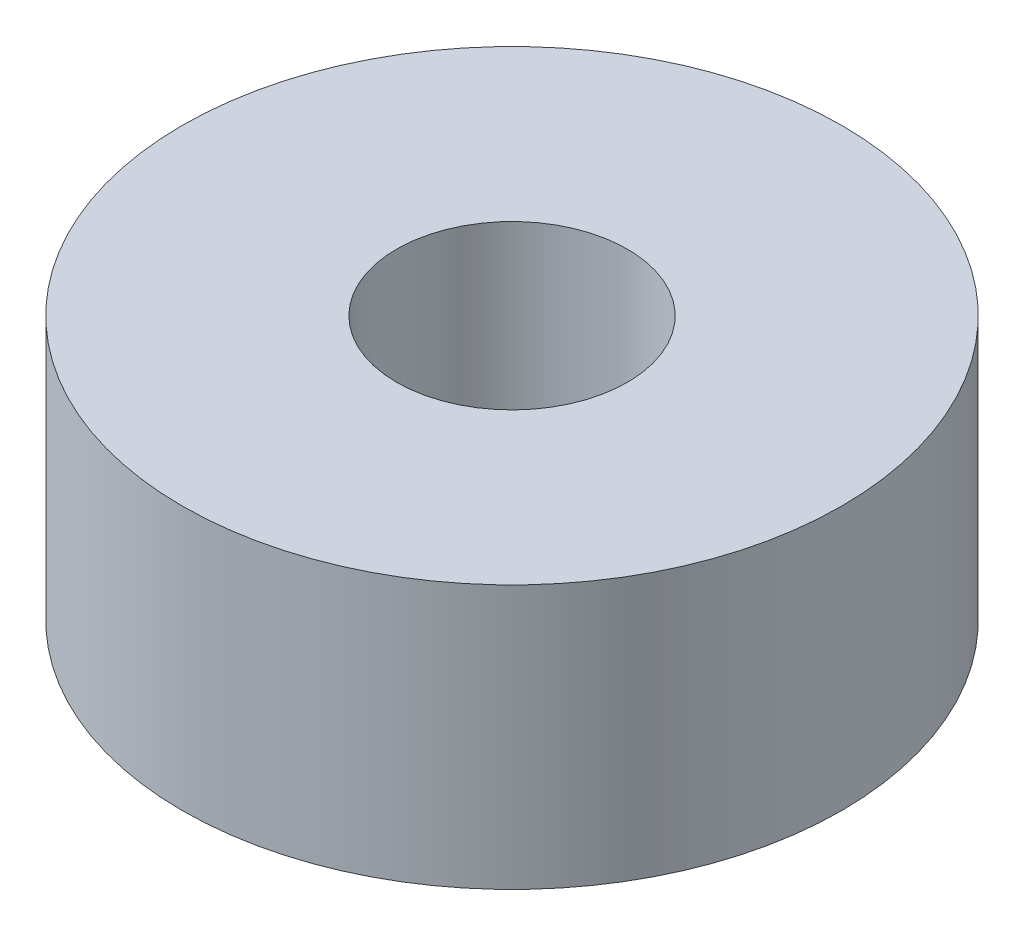
SolidWorks part; units mm, degrees
ref_plane "Front Plane" through (0, 0, 0) normal (0, 0, 1) x (1, 0, 0)
ref_plane "Top Plane" through (0, 0, 0) normal (0, 1, 0) x (1, 0, 0)
ref_plane "Right Plane" through (0, 0, 0) normal (1, 0, 0) x (0, 0, -1)
sketch "Sketch1" plane through (0, 0, 0) normal (0, 1, 0) x (1, 0, 0)
  circle A0 centre (0, 0) radius 5
  circle A1 centre (0, 0) radius 1.75
  dimension "D1" = 10
  dimension "D2" = 3.5
extrude "Boss-Extrude1" add sketch "Sketch1" along normal blind 4
